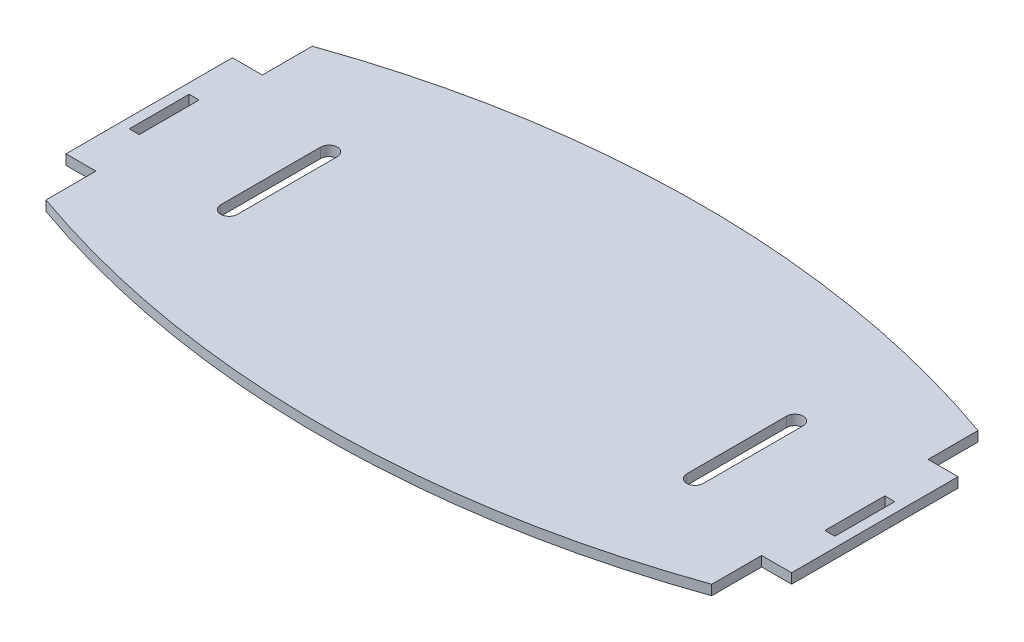
SolidWorks part; units mm, degrees
material "Acrylic (Medium-high impact)"
ref_plane "Front Plane" through (0, 0, 0) normal (0, 0, 1) x (1, 0, 0)
ref_plane "Top Plane" through (0, 0, 0) normal (0, 1, 0) x (1, 0, 0)
ref_plane "Right Plane" through (0, 0, 0) normal (1, 0, 0) x (0, 0, -1)
sketch "Sketch1" plane through (0, 0, 0) normal (0, 1, 0) x (1, 0, 0)
  line L0 (0, -198.9618) -> (0, 247.8058) construction
  line L1 (-304.1511, 0) -> (342.3479, 0) construction
  line L2 (100, 40) -> (-100, 40) construction
  line L3 (-100, 40) -> (-100, 25)
  line L4 (-100, 25) -> (-109, 25)
  line L5 (-109, 25) -> (-109, -25)
  line L6 (-100, -25) -> (-109, -25)
  line L7 (-100, -40) -> (-100, -25)
  line L8 (100, -40) -> (-100, -40) construction
  line L9 (100, -40) -> (100, -25)
  line L10 (100, -25) -> (109, -25)
  line L11 (109, 25) -> (109, -25)
  line L12 (100, 25) -> (109, 25)
  line L13 (100, 40) -> (100, 25)
  line L14 (103, 23.0758) -> (103, -23.1219) construction
  line L15 (106, 18.9582) -> (106, -19.5064) construction
  line L16 (-103, 23.0758) -> (-103, -23.1219) construction
  line L17 (-106, 18.9582) -> (-106, -19.5064) construction
  line L18 (103, -9) -> (103, 9)
  line L19 (103, 9) -> (106, 9)
  line L20 (106, 9) -> (106, -9)
  line L21 (103, -9) -> (106, -9)
  line L22 (-103, 9) -> (-106, 9)
  line L23 (-103, -9) -> (-106, -9)
  line L24 (-106, 9) -> (-106, -9)
  line L25 (-103, -9) -> (-103, 9)
  line L26 (70, 42.6076) -> (70, -40.312) construction
  line L27 (-70, 42.6076) -> (-70, -40.312) construction
  line L28 (-72.5, -15) -> (-72.5, 15)
  line L29 (-67.5, 15) -> (-67.5, -15)
  line L30 (72.5, -15) -> (72.5, 15)
  line L31 (67.5, 15) -> (67.5, -15)
  arc A0 (-72.5, 15) -> (-67.5, 15) centre (-70, 15) cw
  arc A1 (-72.5, -15) -> (-67.5, -15) centre (-70, -15) ccw
  arc A2 (72.5, -15) -> (67.5, -15) centre (70, -15) cw
  arc A3 (72.5, 15) -> (67.5, 15) centre (70, 15) ccw
  arc A4 (-100, 40) -> (100, 40) centre (0, -242.8427) cw
  arc A5 (-100, -40) -> (100, -40) centre (0, 242.8427) ccw
  point P11 (-109, 0)
  point P15 (0, 40)
  point P16 (0, -40)
  point P20 (109, 0)
  point P34 (103, 0)
  point P35 (106, 0)
  point P41 (100, -32.5)
  point P49 (-72.5, 0)
  point P52 (-67.5, 0)
  dimension "D12" = 300
  dimension "D1" = 200
  dimension "D2" = 80
  dimension "D3" = 9
  dimension "D4" = 50
  dimension "D5" = 3
  dimension "D6" = 3
  dimension "D7" = 9
  dimension "D8" = 30
  dimension "D9" = 15
  dimension "D10" = 2.5
  dimension "D11" = 2.5
extrude "Boss-Extrude1" add sketch "Sketch1" along normal blind 3
